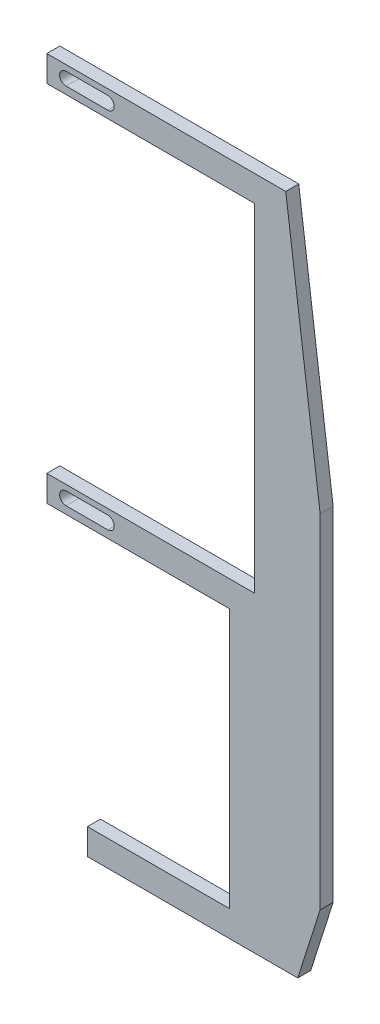
SolidWorks part; units mm, degrees
ref_plane "Front Plane" through (0, 0, 0) normal (0, 0, 1) x (1, 0, 0)
ref_plane "Top Plane" through (0, 0, 0) normal (0, 1, 0) x (1, 0, 0)
ref_plane "Right Plane" through (0, 0, 0) normal (1, 0, 0) x (0, 0, -1)
sketch "Sketch1" plane through (0, 0, 0) normal (0, 0, 1) x (1, 0, 0)
  line L0 (0, 0) -> (50.8, 0)
  line L1 (50.8, 0) -> (50.8, -82.55)
  line L2 (50.8, -82.55) -> (0, -82.55)
  line L3 (0, -82.55) -> (0, -88.9)
  line L10 (66.8335, -57.7192) -> (58.42, 6.35)
  line L11 (58.42, 6.35) -> (0, 6.35)
  line L12 (0, 6.35) -> (0, 0)
  line L15 (66.8335, -141.5754) -> (66.8335, -57.7192)
  line L17 (0, -88.9) -> (44.7212, -88.9)
  line L18 (44.7212, -88.9) -> (44.7212, -152.4)
  line L19 (44.7212, -152.4) -> (9.9282, -152.4)
  line L20 (9.9282, -152.4) -> (9.9282, -158.75)
  line L21 (9.9282, -158.75) -> (61.3452, -158.75)
  line L22 (61.3452, -158.75) -> (66.8335, -141.5754)
  dimension "D1" = 6.35
  dimension "D2" = 6.35
  dimension "D3" = 6.35
  dimension "D4" = 82.55
  dimension "D5" = 50.8
  dimension "D6" = 58.42
  dimension "D7" = 63.5
extrude "Boss-Extrude1" add sketch "Sketch1" along normal blind 3.175 contours L11 L12 L0 L1 L2 L3 L17 L18 L19 L20 L21 L22 L15 L10
sketch "Sketch2" plane through (0, 0, 3.175) normal (0, 0, 1) x (1, 0, 0)
  line L0 (4.6961, 3.3683) -> (14.8938, 3.3683) construction
  line L1 (4.6961, 4.9365) -> (14.8938, 4.9365)
  line L2 (4.6961, 1.8) -> (14.8938, 1.8)
  line L3 (4.6961, -85.4979) -> (14.8938, -85.4979) construction
  line L4 (4.6961, -83.9297) -> (14.8938, -83.9297)
  line L5 (4.6961, -87.0662) -> (14.8938, -87.0662)
  arc A0 (4.6961, 4.9365) -> (4.6961, 1.8) centre (4.6961, 3.3683) ccw
  arc A1 (14.8938, 1.8) -> (14.8938, 4.9365) centre (14.8938, 3.3683) ccw
  arc A2 (4.6961, -83.9297) -> (4.6961, -87.0662) centre (4.6961, -85.4979) ccw
  arc A3 (14.8938, -87.0662) -> (14.8938, -83.9297) centre (14.8938, -85.4979) ccw
  point P2 (9.795, 3.3683)
  point P7 (9.795, -85.4979)
extrude "Cut-Extrude1" cut sketch "Sketch2" against normal through all
